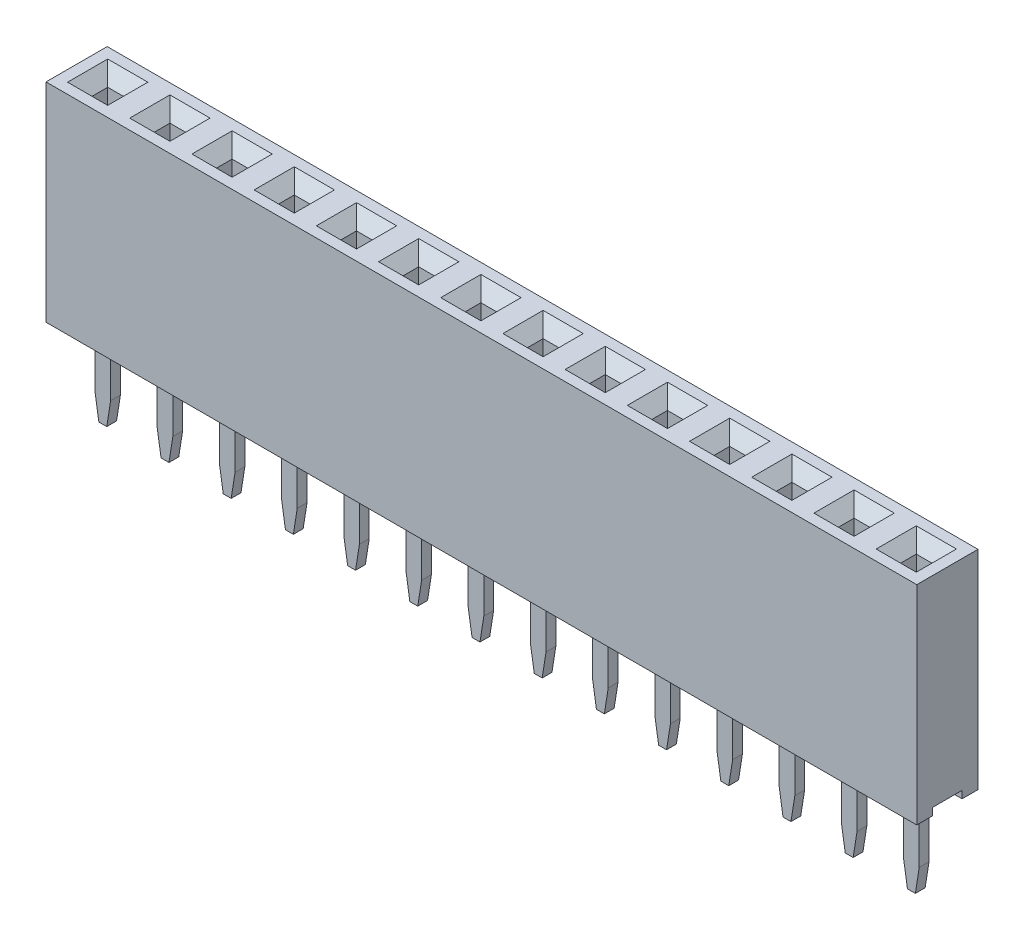
SolidWorks part; units mm, degrees
ref_plane "Front Plane" through (0, 0, 0) normal (0, 0, 1) x (1, 0, 0)
ref_plane "Top Plane" through (0, 0, 0) normal (0, 1, 0) x (1, 0, 0)
ref_plane "Right Plane" through (0, 0, 0) normal (1, 0, 0) x (0, 0, -1)
sketch "Sketch1" plane through (0, 0, 0) normal (0, 1, 0) x (1, 0, 0)
  line L1 (-1.27, -1.25) -> (1.27, -1.25)
  line L2 (-1.27, -1.25) -> (-1.27, 1.25)
  line L3 (-1.27, 1.25) -> (1.27, 1.25)
  line L4 (1.27, -1.25) -> (1.27, 1.25)
  line L5 (-1.27, -1.25) -> (1.27, 1.25) construction
  line L6 (-1.27, 1.25) -> (1.27, -1.25) construction
  point P0 (0, 0)
  dimension "D1" = 2.54
  dimension "D2" = 2.5
extrude "Boss-Extrude1" add sketch "Sketch1" along normal blind 8.5
sketch "Sketch2" plane through (0, 0, 0) normal (0, -1, 0) x (1, 0, 0)
  line L1 (1.27, 1.25) -> (1.27, -1.25) construction
  line L2 (-1.27, -0.6) -> (1.27, -0.6)
  line L3 (-1.27, -0.6) -> (-1.27, 0.6)
  line L4 (-1.27, 0.6) -> (1.27, 0.6)
  line L5 (1.27, -0.6) -> (1.27, 0.6)
  line L6 (-1.27, -0.6) -> (1.27, 0.6) construction
  line L7 (-1.27, 0.6) -> (1.27, -0.6) construction
  point P2 (0, 0)
  dimension "D1" = 1.2
extrude "Cut-Extrude1" cut sketch "Sketch2" against normal blind 0.3
sketch "Sketch3" plane through (0, 8.5, 0) normal (0, 1, 0) x (1, 0, 0)
  line L1 (-0.32, -0.32) -> (0.32, -0.32)
  line L2 (-0.32, -0.32) -> (-0.32, 0.32)
  line L3 (-0.32, 0.32) -> (0.32, 0.32)
  line L4 (0.32, -0.32) -> (0.32, 0.32)
  line L5 (-0.32, -0.32) -> (0.32, 0.32) construction
  line L6 (-0.32, 0.32) -> (0.32, -0.32) construction
  point P0 (0, 0)
  dimension "D1" = 0.64
  dimension "D2" = 0.64
extrude "Cut-Extrude2" cut sketch "Sketch3" against normal blind 6 and the other way through all
chamfer "Chamfer1" distance 0.5 angle 45 4 edges at (0, 8.5, -0.32) (-0.32, 8.5, 0) (0, 8.5, 0.32) (0.32, 8.5, 0)
sketch "Sketch4" plane through (0, 0.3, 0) normal (0, -1, 0) x (1, 0, 0)
  line L1 (-0.32, -0.2) -> (0.32, -0.2)
  line L2 (-0.32, -0.2) -> (-0.32, 0.2)
  line L3 (-0.32, 0.2) -> (0.32, 0.2)
  line L4 (0.32, -0.2) -> (0.32, 0.2)
  line L5 (-0.32, -0.2) -> (0.32, 0.2) construction
  line L6 (-0.32, 0.2) -> (0.32, -0.2) construction
  point P0 (0, 0)
  dimension "D1" = 0.4
  dimension "D2" = 0.64
extrude "Boss-Extrude2" add sketch "Sketch4" along normal blind 3.8
chamfer "Chamfer2" distance 1 angle 9 2 edges at (-0.32, -3.5, 0) (0.32, -3.5, 0)
pattern_linear "LPattern1" count 14 spacing 2.54 along (-1, 0, 0) of "Boss-Extrude1", "Cut-Extrude1", "Cut-Extrude2", "Chamfer1", "Boss-Extrude2", "Chamfer2"
